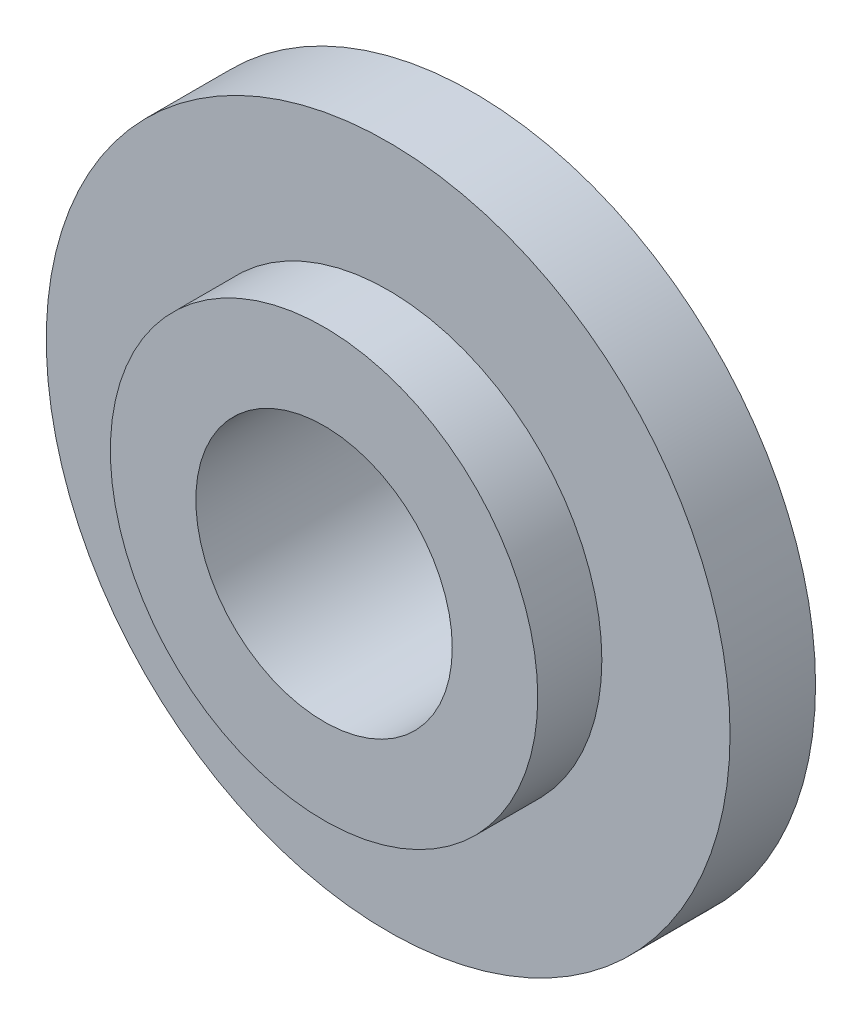
SolidWorks part; units mm, degrees
ref_plane "前视基准面" through (0, 0, 0) normal (0, 0, 1) x (1, 0, 0)
ref_plane "上视基准面" through (0, 0, 0) normal (0, 1, 0) x (1, 0, 0)
ref_plane "右视基准面" through (0, 0, 0) normal (1, 0, 0) x (0, 0, -1)
sketch "草图1" plane through (0, 0, 0) normal (0, 0, 1) x (1, 0, 0)
  circle A0 centre (0, 0) radius 30
  circle A1 centre (0, 0) radius 50
  dimension "D1" = 60
  dimension "D2" = 100
extrude "凸台-拉伸1" add sketch "草图1" along normal mid plane 50
sketch "草图2" plane through (0, 0, 0) normal (0, 0, 1) x (1, 0, 0)
  circle A0 centre (0, 0) radius 80
  circle A1 centre (0, 0) radius 50 construction
  circle A2 centre (0, 0) radius 50
  dimension "D1" = 160
extrude "凸台-拉伸2" add sketch "草图2" along normal mid plane 20
